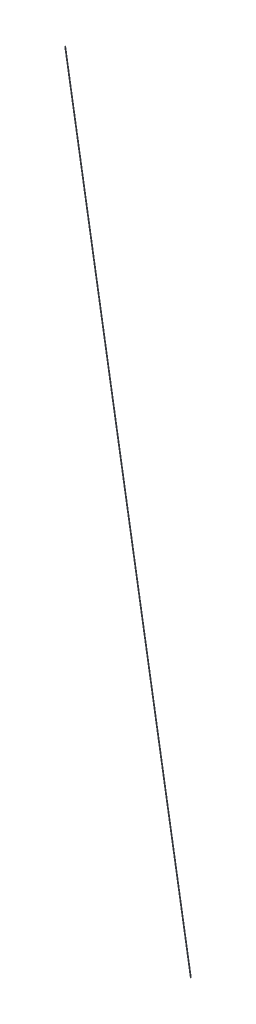
SolidWorks part; units mm, degrees
ref_plane "前视基准面" through (0, 0, 0) normal (0, 0, 1) x (1, 0, 0)
ref_plane "上视基准面" through (0, 0, 0) normal (0, 1, 0) x (1, 0, 0)
ref_plane "右视基准面" through (0, 0, 0) normal (1, 0, 0) x (0, 0, -1)
sketch "草图1" plane through (0, 0, 0) normal (0, 1, 0) x (1, 0, 0)
  line L0 (0, 0) -> (0, -217.5)
sketch "草图2" plane through (0, 0, 0) normal (0, 0, 1) x (1, 0, 0)
  line L0 (0, 0) -> (0, 500)
sketch "草图3" plane through (0, 0, 0) normal (1, 0, 0) x (0, 0, -1)
  line L9 (0, 0) -> (-217.5, 1505)
sweep "扫描1" add path "草图3" circular profile diameter 1 parameters "D3"=1
